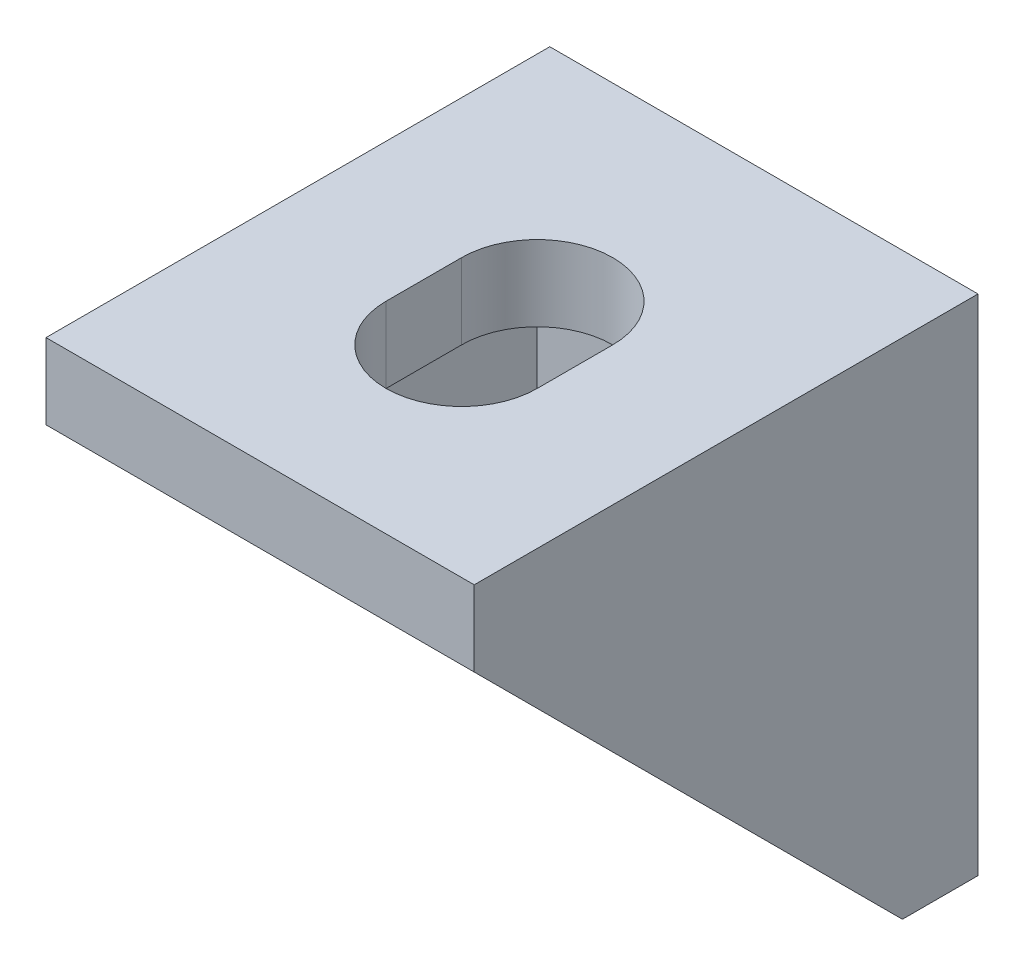
SolidWorks part; units mm, degrees
material "1060 Alloy"
ref_plane "Front Plane" through (0, 0, 0) normal (0, 0, 1) x (1, 0, 0)
ref_plane "Top Plane" through (0, 0, 0) normal (0, 1, 0) x (1, 0, 0)
ref_plane "Right Plane" through (0, 0, 0) normal (1, 0, 0) x (0, 0, -1)
sketch "Sketch1" plane through (0, 0, 0) normal (1, 0, 0) x (0, 0, -1)
  line L0 (0, 0) -> (-20, 0)
  line L1 (-20, 0) -> (-20, -3)
  line L2 (-20, -3) -> (-11.5, -11.5)
  line L3 (-11.5, -11.5) -> (0, 0) construction
  line L4 (-3, -20) -> (-11.5, -11.5)
  line L5 (0, -20) -> (-3, -20)
  line L6 (0, 0) -> (0, -20)
  dimension "D1" = 3
  dimension "D2" = 20
extrude "Boss-Extrude1" add sketch "Sketch1" along normal mid plane 17
sketch "Sketch2" plane through (0, 0, 0) normal (1, 0, 0) x (0, 0, -1)
  line L0 (-20, -3) -> (-3, -20) construction
  line L1 (-3, -3) -> (-20, -3)
  line L2 (-3, -3) -> (-3, -20)
  line L3 (-3, -20) -> (-20, -20)
  line L4 (-20, -3) -> (-20, -20)
  line L5 (-20, 0) -> (-20, -3) construction
extrude "Cut-Extrude1" cut sketch "Sketch2" against normal mid plane 12
sketch "Sketch3" plane through (0, 0, 3) normal (0, 0, 1) x (1, 0, 0)
  line L0 (0, -9) -> (0, -12) construction
  line L1 (-3, -9) -> (-3, -12)
  line L2 (3, -9) -> (3, -12)
  line L3 (0, -10.5) -> (0.7454, -10.5) construction
  line L4 (-6, -20) -> (6, -20) construction
  arc A0 (-3, -9) -> (3, -9) centre (0, -9) cw
  arc A1 (-3, -12) -> (3, -12) centre (0, -12) ccw
  dimension "D3" = 9
  dimension "D4" = 5
  dimension "D1" = 3
  dimension "D2" = 3
extrude "Cut-Extrude2" cut sketch "Sketch3" against normal up to next (3 mm away)
sketch "Sketch4" plane through (0, 0, 0) normal (0, 0, -1) x (-1, 0, 0)
  line L0 (-1, -2.15) -> (1, -2.15) construction
  line L1 (-1, -3) -> (1, -3)
  line L2 (-1, -1.3) -> (1, -1.3)
  line L3 (0, 0) -> (0, -2.15) construction
  line L4 (-8.5, 0) -> (8.5, 0) construction
  line L5 (-2.1032, -9.8) -> (3, -9.8) construction
  line L6 (-1, -18.3) -> (1, -18.3)
  line L7 (-1, -16.6) -> (1, -16.6)
  line L8 (3, -12) -> (3, -9) construction
  arc A0 (-1, -3) -> (-1, -1.3) centre (-1, -2.15) cw
  arc A1 (1, -3) -> (1, -1.3) centre (1, -2.15) ccw
  arc A2 (1, -16.6) -> (1, -18.3) centre (1, -17.45) cw
  arc A3 (-1, -16.6) -> (-1, -18.3) centre (-1, -17.45) ccw
  dimension "D3" = 3.7
  dimension "D4" = 3
  dimension "D5" = 17
  dimension "D1" = 0.85
  dimension "D2" = 0.85
ref_plane "Plane1" through (0, 0, 0) normal (0, 0.7071, 0.7071) x (-1, 0, 0)
mirror "Mirror1" about plane through (0, 0, 0) normal (0, 0.7071, 0.7071) of "Cut-Extrude2"
